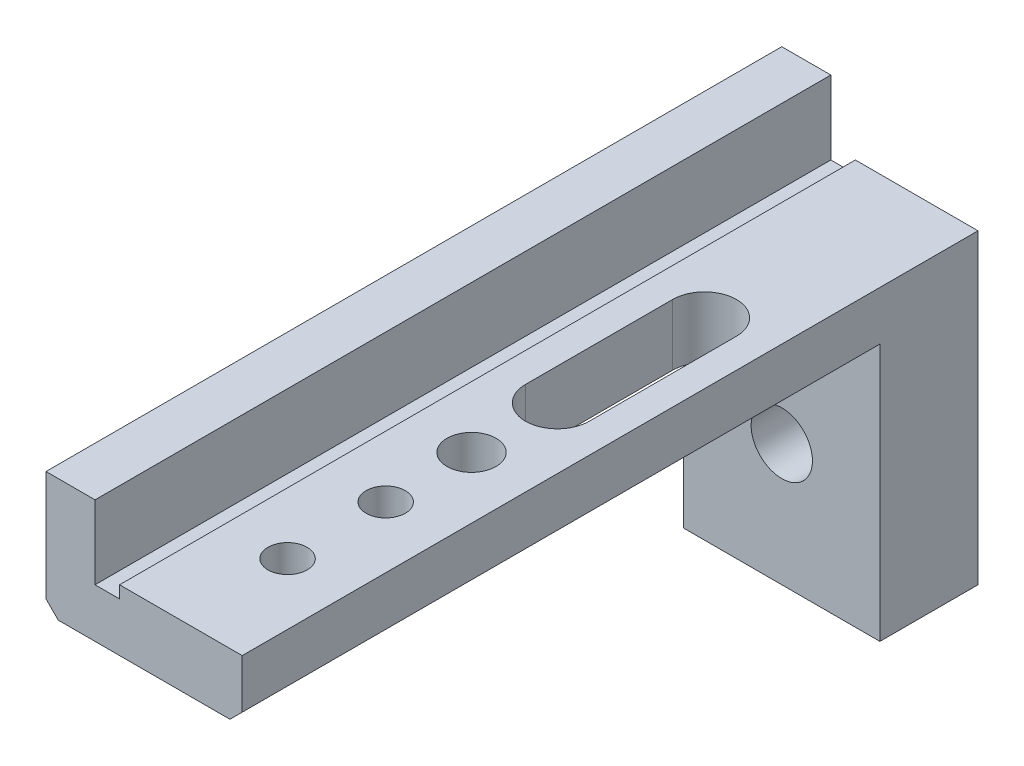
SolidWorks part; units mm, degrees
ref_plane "Front Plane" through (0, 0, 0) normal (0, 0, 1) x (1, 0, 0)
ref_plane "Top Plane" through (0, 0, 0) normal (0, 1, 0) x (1, 0, 0)
ref_plane "Right Plane" through (0, 0, 0) normal (1, 0, 0) x (0, 0, -1)
sketch "Sketch1" plane through (0, 0, 0) normal (0, 0, 1) x (1, 0, 0)
  line L1 (-5.1525, 3) -> (-3.1525, 3)
  line L2 (-5.1525, 3) -> (-5.1525, -2)
  line L4 (-3.1525, 3) -> (-3.1525, 0)
  line L5 (-5.1525, -2) -> (2.8475, -2)
  line L7 (-2.1525, 0.5) -> (2.8475, 0.5)
  line L8 (2.8475, -2) -> (2.8475, 0.5)
  line L9 (-3.1525, 0) -> (-2.1525, 0)
  line L10 (-2.1525, 0) -> (-2.1525, 0.5)
  point P8 (-5.1525, -0.1556)
  dimension "D1" = 2
  dimension "D2" = 1
  dimension "D3" = 0.5
  dimension "D4" = 8
  dimension "D5" = 5
  dimension "D6" = 2.5
extrude "Boss-Extrude1" add sketch "Sketch1" along normal blind 30
sketch "Sketch2" plane through (0, -2, 0) normal (0, -1, 0) x (1, 0, 0)
  line L0 (2.8475, 30) -> (2.8475, 0) construction
  line L1 (-5.1525, 0) -> (2.8475, 0)
  line L2 (-5.1525, 0) -> (-5.1525, 4)
  line L3 (-5.1525, 4) -> (2.8475, 4)
  line L4 (2.8475, 0) -> (2.8475, 4)
  dimension "D1" = 4
extrude "Boss-Extrude2" add sketch "Sketch2" along normal blind 10
sketch "Sketch3" plane through (0, 0.5, 0) normal (0, 1, 0) x (1, 0, 0)
  line L0 (0.3475, -14.65) -> (0.3475, -8.65) construction
  line L1 (-0.9525, -14.65) -> (-0.9525, -8.65)
  line L2 (1.6475, -14.65) -> (1.6475, -8.65)
  line L3 (2.8475, 0) -> (-2.1525, 0) construction
  line L4 (-5.1525, -30) -> (-5.1525, 0) construction
  circle A0 centre (0.3475, -18.15) radius 1
  arc A1 (-0.9525, -14.65) -> (1.6475, -14.65) centre (0.3475, -14.65) ccw
  arc A2 (1.6475, -8.65) -> (-0.9525, -8.65) centre (0.3475, -8.65) ccw
  point P4 (0.3475, -11.65)
  point P11 (0, 0)
  point P13 (0.7141, -8.8601)
  dimension "D2" = 1.3
  dimension "D6" = 2
  dimension "D1" = 6
  dimension "D3" = 8.65
  dimension "D4" = 5.5
  dimension "D5" = 18.15
extrude "Cut-Extrude1" cut sketch "Sketch3" against normal blind 10
hole_wizard "M2 Tapped Hole1" positions "Sketch4" profile "Sketch5" tap size "M2" standard "ISO"
sketch "Sketch4" plane through (0, 0.5, 0) normal (0, 1, 0) x (1, 0, 0)
  line L0 (-5.1525, -30) -> (-5.1525, 0) construction
  line L1 (2.8475, 0) -> (-2.1525, 0) construction
  point P0 (0.3475, -21.65)
  point P2 (0.3475, -25.65)
  point P5 (0, 0)
  dimension "D1" = 5.5
  dimension "D2" = 21.65
  dimension "D3" = 25.65
sketch "Sketch5" plane through (0.3475, 0.5, 21.65) normal (1, 0, 0) x (0, 0, 1)
  line L0 (0, 0) -> (0, 5.6807)
  line L1 (0, 5.6807) -> (0.8, 5.2)
  line L2 (0.8, 5.2) -> (0.8, 0)
  line L5 (0.8, 0) -> (0, 0)
  line L10 (0, 5.6807) -> (-0.8, 5.2) construction
  line L11 (0, -6.35) -> (0, 107.95) construction
  dimension "Tap Drill Dia." = 1.6
  dimension "Tap Drill Depth" = 5.2
  dimension "Drill Angle" = 118
cosmetic thread "Hole Thread1" parameters "D1"=2.5, "D2"=2
cosmetic thread "Hole Thread2" parameters "D1"=2.5, "D2"=2
hole_wizard "M3 Tapped Hole1" positions "Sketch7" profile "Sketch8" tap size "M3" standard "ISO"
sketch "Sketch7" plane through (0, 0, 4) normal (0, 0, 1) x (1, 0, 0)
  line L0 (2.8475, -12) -> (-5.1525, -12) construction
  point P0 (-1.1525, -7)
  dimension "D1" = 5
sketch "Sketch8" plane through (-1.1525, -7, 4) normal (1, 0, 0) x (0, -1, 0)
  line L0 (0, 0) -> (0, 8.2511)
  line L1 (0, 8.2511) -> (1.25, 7.5)
  line L2 (1.25, 7.5) -> (1.25, 0)
  line L5 (1.25, 0) -> (0, 0)
  line L10 (0, 8.2511) -> (-1.25, 7.5) construction
  line L11 (0, -6.35) -> (0, 107.95) construction
  dimension "Tap Drill Dia." = 2.5
  dimension "Tap Drill Depth" = 7.5
  dimension "Drill Angle" = 118
cosmetic thread "Hole Thread3" parameters "D1"=4, "D2"=3
chamfer "Chamfer1" distance 0.5 angle 45 2 edges at (-5.1525, -2, 17) (2.8475, -2, 17)
